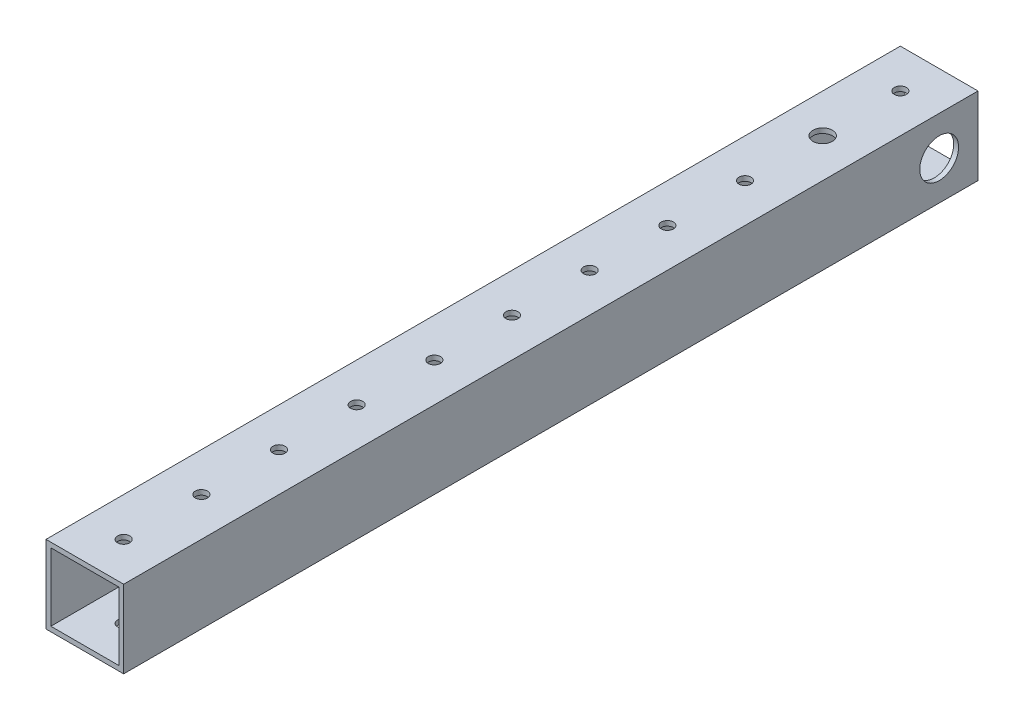
SolidWorks part; units mm, degrees
ref_plane "Front Plane" through (0, 0, 0) normal (0, 0, 1) x (1, 0, 0)
ref_plane "Top Plane" through (0, 0, 0) normal (0, 1, 0) x (1, 0, 0)
ref_plane "Right Plane" through (0, 0, 0) normal (1, 0, 0) x (0, 0, -1)
sketch "Sketch1" plane through (0, 0, 0) normal (0, 0, 1) x (1, 0, 0)
  line L1 (-11.1125, 11.1125) -> (11.1125, 11.1125)
  line L2 (-11.1125, 11.1125) -> (-11.1125, -11.1125)
  line L3 (-11.1125, -11.1125) -> (11.1125, -11.1125)
  line L4 (11.1125, 11.1125) -> (11.1125, -11.1125)
  line L5 (-11.1125, 11.1125) -> (11.1125, -11.1125) construction
  line L6 (-11.1125, -11.1125) -> (11.1125, 11.1125) construction
  line L7 (-12.7, 12.7) -> (12.7, 12.7)
  line L8 (-12.7, 12.7) -> (-12.7, -12.7)
  line L9 (-12.7, -12.7) -> (12.7, -12.7)
  line L10 (12.7, 12.7) -> (12.7, -12.7)
  line L11 (-12.7, 12.7) -> (12.7, -12.7) construction
  line L12 (-12.7, -12.7) -> (12.7, 12.7) construction
  point P0 (0, 0)
  point P6 (0, 0)
  dimension "D1" = 25.4
  dimension "D2" = 25.4
  dimension "D3" = 1.5875
extrude "Boss-Extrude1" add sketch "Sketch1" along normal blind 279.4
sketch "Sketch2" plane through (0, 12.7, 0) normal (0, 1, 0) x (1, 0, 0)
  line L0 (0, -279.4) -> (0, -266.7) construction
  line L1 (12.7, -279.4) -> (-12.7, -279.4) construction
  circle A0 centre (0, -266.7) radius 1.9844
  circle A1 centre (0, -241.3) radius 1.9844
  circle A2 centre (0, -215.9) radius 1.9844
  circle A3 centre (0, -190.5) radius 1.9844
  circle A4 centre (0, -165.1) radius 1.9844
  circle A5 centre (0, -139.7) radius 1.9844
  circle A6 centre (0, -114.3) radius 1.9844
  circle A7 centre (0, -88.9) radius 1.9844
  circle A8 centre (0, -63.5) radius 1.9844
  circle A9 centre (0, -38.1) radius 1.9844
  circle A10 centre (0, -12.7) radius 1.9844
  circle A11 centre (0, 12.7) radius 1.9844
  dimension "D2" = 3.9688
  dimension "D1" = 12.7
  dimension "D3" = 12
extrude "Cut-Extrude1" cut sketch "Sketch2" against normal through all
sketch "Sketch3" plane through (0, 12.7, 0) normal (0, 1, 0) x (1, 0, 0)
  circle A0 centre (0, -38.1) radius 3.175
  circle A4 centre (0, -38.1) radius 1.9844 construction
  dimension "D1" = 6.35
extrude "Cut-Extrude2" cut sketch "Sketch3" against normal through all
sketch "Sketch4" plane through (12.7, 0, 0) normal (1, 0, 0) x (0, 0, -1)
  line L0 (0, 0) -> (-12.7, 0) construction
  line L1 (0, -12.7) -> (0, 12.7) construction
  circle A0 centre (-12.7, 0) radius 6.35
  dimension "D2" = 12.7
  dimension "D1" = 12.7
extrude "Cut-Extrude3" cut sketch "Sketch4" against normal through all
